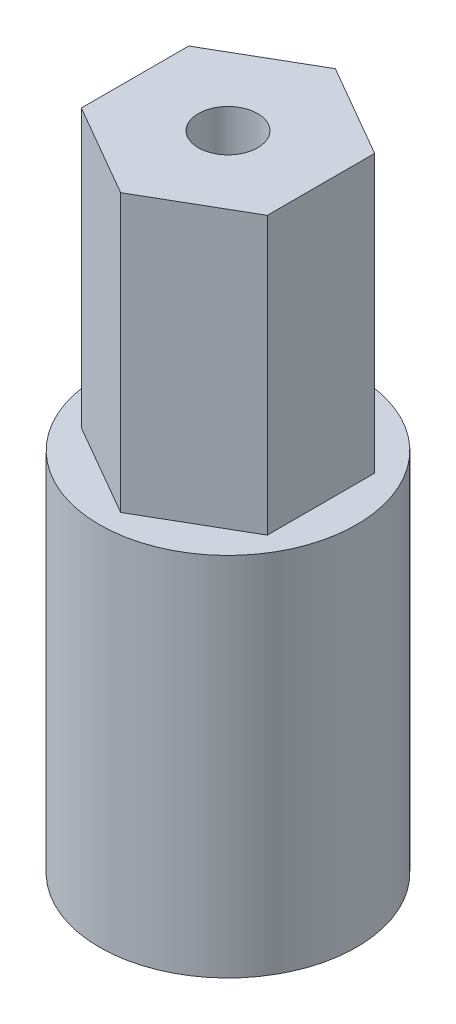
SolidWorks part; units mm, degrees
ref_plane "Front Plane" through (0, 0, 0) normal (0, 0, 1) x (1, 0, 0)
ref_plane "Top Plane" through (0, 0, 0) normal (0, 1, 0) x (1, 0, 0)
ref_plane "Right Plane" through (0, 0, 0) normal (1, 0, 0) x (0, 0, -1)
sketch "Sketch1" plane through (0, 0, 0) normal (0, 1, 0) x (1, 0, 0)
  circle A2 centre (0, 0) radius 8.255
  dimension "D3" = 16.51
extrude "Boss-Extrude1" add sketch "Sketch1" along normal blind 23.495
sketch "Sketch9" plane through (0, 23.495, 0) normal (0, 1, 0) x (1, 0, 0)
  line L2 (0, 6.8924) -> (-5.969, 3.4462)
  line L3 (-5.969, 3.4462) -> (-5.969, -3.4462)
  line L4 (-5.969, -3.4462) -> (0, -6.8924)
  line L5 (0, -6.8924) -> (5.969, -3.4462)
  line L6 (5.969, -3.4462) -> (5.969, 3.4462)
  line L7 (5.969, 3.4462) -> (0, 6.8924)
  circle A0 centre (0, 0) radius 5.969 construction
  circle A1 centre (0, 0) radius 1.905
  dimension "D1" = 11.938
  dimension "D2" = 3.81
extrude "Boss-Extrude6" add sketch "Sketch9" along normal blind 17.78
